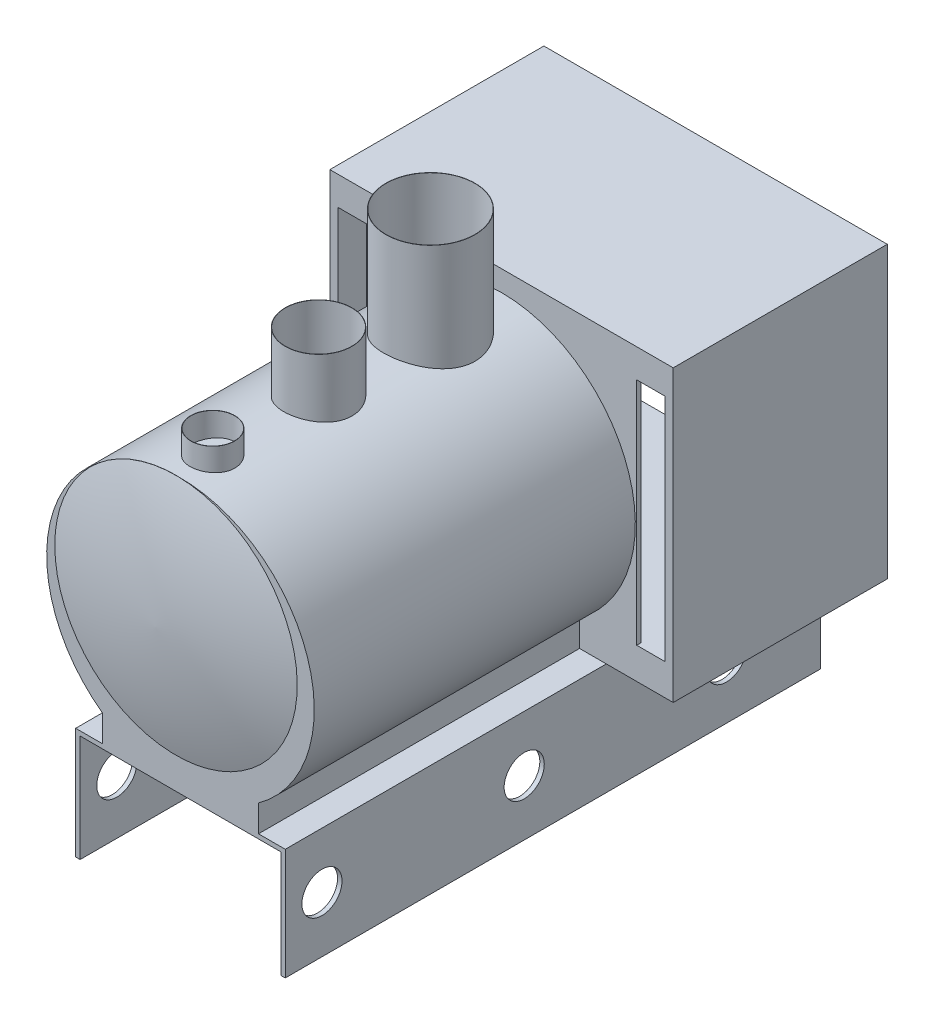
SolidWorks part; units mm, degrees
ref_plane "Front Plane" through (0, 0, 0) normal (0, 0, 1) x (1, 0, 0)
ref_plane "Top Plane" through (0, 0, 0) normal (0, 1, 0) x (1, 0, 0)
ref_plane "Right Plane" through (0, 0, 0) normal (1, 0, 0) x (0, 0, -1)
sketch "Sketch1" plane through (0, 0, 0) normal (0, 0, 1) x (1, 0, 0)
  line L0 (0, 0) -> (0, 1270)
  line L1 (0, 1270) -> (-2387.6, 1270)
  line L2 (-2387.6, 1270) -> (-2387.6, 0)
  line L3 (-2387.6, 0) -> (-2336.8, 0)
  line L4 (-2336.8, 0) -> (-2336.8, 1219.2)
  line L5 (-2336.8, 1219.2) -> (-50.8, 1219.2)
  line L6 (-50.8, 1219.2) -> (-50.8, 0)
  line L7 (-50.8, 0) -> (0, 0)
  line L8 (-1193.8, 1270) -> (-1193.8, 762) construction
  line L9 (-2336.8, 0) -> (-50.8, 0) construction
  line L10 (-2082.8, 1574.8) -> (-2082.8, 1270)
  line L11 (-304.8, 1574.8) -> (-304.8, 1270)
  line L12 (-1193.8, 0) -> (-1193.8, 1270) construction
  line L13 (-2082.8, 1574.8) -> (-304.8, 1574.8) construction
  arc A0 (-304.8, 1574.8) -> (-2082.8, 1574.8) centre (-1193.8, 2812.6429) ccw
  dimension "D7" = 1524
  dimension "D1" = 50.8
  dimension "D2" = 50.8
  dimension "D3" = 50.8
  dimension "D4" = 2286
  dimension "D5" = 1778
  dimension "D6" = 762
  dimension "D8" = 304.8
  dimension "D9" = 1219.2
extrude "Boss-Extrude3" add sketch "Sketch1" against normal blind 3657.6 contours L11 A0 L10 L1
sketch "Sketch2" plane through (0, 0, -3657.6) normal (0, 0, -1) x (-1, 0, 0)
  line L0 (0, 1270) -> (0, 0)
  line L1 (0, 0) -> (50.8, 0)
  line L2 (50.8, 0) -> (50.8, 1219.2)
  line L3 (50.8, 1219.2) -> (2336.8, 1219.2)
  line L4 (2336.8, 1219.2) -> (2336.8, 0)
  line L5 (2336.8, 0) -> (2387.6, 0)
  line L6 (2387.6, 0) -> (2387.6, 1270)
  line L7 (2387.6, 1270) -> (3149.6, 1270)
  line L8 (3149.6, 1270) -> (3149.6, 4572)
  line L9 (3149.6, 4572) -> (-762, 4572)
  line L10 (-762, 4572) -> (-762, 1270)
  line L11 (-762, 1270) -> (0, 1270)
  line L12 (1193.8, 1219.2) -> (1193.8, 4572) construction
  line L13 (-346.365, 1626.9817) -> (2733.965, 1626.9817) construction
  line L14 (-666.365, 4245.6965) -> (-346.365, 4245.6965)
  line L15 (-666.365, 4245.6965) -> (-666.365, 1626.9817)
  line L16 (-666.365, 1626.9817) -> (-346.365, 1626.9817)
  line L17 (-346.365, 4245.6965) -> (-346.365, 1626.9817)
  line L18 (2733.965, 4245.6965) -> (3053.965, 4245.6965)
  line L19 (2733.965, 4245.6965) -> (2733.965, 1626.9817)
  line L20 (2733.965, 1626.9817) -> (3053.965, 1626.9817)
  line L21 (3053.965, 4245.6965) -> (3053.965, 1626.9817)
  line L22 (1193.8, 1626.9817) -> (1193.8, 1219.2) construction
  dimension "D1" = 762
  dimension "D2" = 3302
  dimension "D3" = 3080.33
  dimension "D4" = 320
  dimension "D5" = 320
extrude "Boss-Extrude4" add sketch "Sketch2" along normal blind 2438.4
sketch "Sketch4" plane through (0, 0, -6096) normal (0, 0, -1) x (-1, 0, 0)
  line L1 (-346.365, 4245.6965) -> (2733.965, 4245.6965)
  line L2 (-346.365, 4245.6965) -> (-346.365, 1626.9817)
  line L3 (-346.365, 1626.9817) -> (2733.965, 1626.9817)
  line L4 (2733.965, 4245.6965) -> (2733.965, 1626.9817)
extrude "Cut-Extrude1" cut sketch "Sketch4" against normal blind 2387.6
sketch "Sketch5" plane through (0, 0, 0) normal (1, 0, 0) x (0, 0, -1)
  line L0 (0, 635) -> (6096, 635) construction
  line L1 (0, 0) -> (0, 1270) construction
  line L2 (6096, 1270) -> (6096, 0) construction
  circle A0 centre (5026.0572, 635) radius 228.6
  circle A1 centre (2722.0572, 635) radius 228.6
  circle A2 centre (418.0572, 635) radius 228.6
  dimension "D1" = 457.2
  dimension "D2" = 2304
  dimension "D3" = 2304
sketch "Sketch6" plane through (0, 0, 0) normal (1, 0, 0) x (0, 0, -1)
extrude "Cut-Extrude2" cut sketch "Sketch5" against normal blind 4484.116 and the other way blind 2115.312
ref_plane "Plane3" through (-1244.6, 0, 0) normal (-1, 0, 0) x (0, 0, 1)
sketch "Sketch9" plane through (-1244.6, 0, 0) normal (-1, 0, 0) x (0, 0, 1)
  line L0 (-418.7486, 4552.9006) -> (-418.7486, 3620.9798) construction
  line L1 (-669.7572, 3620.9798) -> (-669.7572, 4591.7678)
  dimension "D1" = 254
revolve "Revolve-Thin2" add sketch "Sketch9" angle 360 about L0
sketch "Sketch10" plane through (-1244.6, 0, 0) normal (-1, 0, 0) x (0, 0, 1)
  line L0 (-1624.0824, 4987.4719) -> (-1624.0824, 3831.2639) construction
  line L1 (-1243.0824, 4987.4719) -> (-1243.0824, 3831.2639)
  dimension "D1" = 762
revolve "Revolve-Thin3" add sketch "Sketch10" angle 360 about L0
sketch "Sketch11" plane through (-1244.6, 0, 0) normal (-1, 0, 0) x (0, 0, 1)
  line L0 (-2898.6398, 5515.8357) -> (-2898.6398, 3788.6357) construction
  line L1 (-2390.6398, 5515.8357) -> (-2390.6398, 3788.6357)
  dimension "D1" = 508
revolve "Revolve-Thin4" add sketch "Sketch11" angle 360 about L0
sketch "Sketch13" plane through (-1244.6, 0, 0) normal (-1, 0, 0) x (0, 0, 1)
  line L0 (0, 2955.7214) -> (231.8991, 2955.7214)
  line L1 (0, 1574.8) -> (0, 4336.6429) construction
  arc A0 (0, 4336.6429) -> (231.8991, 2955.7214) centre (-4706.1046, 2836.4114) cw
revolve "Revolve-Thin5" add sketch "Sketch13" angle 360 about L0 wall 2.54
